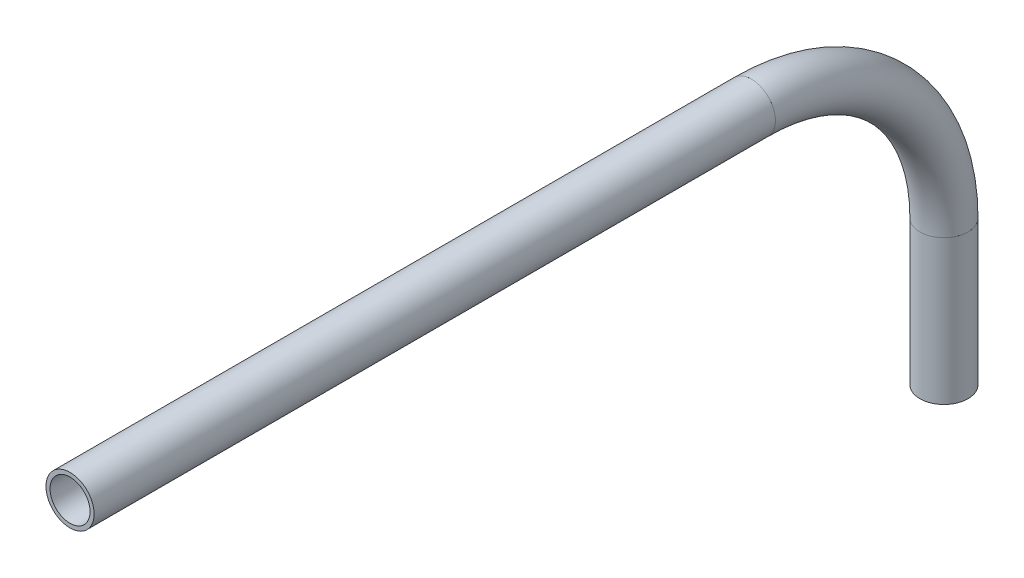
SolidWorks part; units mm, degrees
ref_plane "Front Plane" through (0, 0, 0) normal (0, 0, 1) x (1, 0, 0)
ref_plane "Top Plane" through (0, 0, 0) normal (0, 1, 0) x (1, 0, 0)
ref_plane "Right Plane" through (0, 0, 0) normal (1, 0, 0) x (0, 0, -1)
sketch "Sketch1" plane through (0, 0, 0) normal (1, 0, 0) x (0, 0, -1)
  line L1 (-129.6392, -232.8178) -> (-309.3187, -232.8178)
  line L2 (-78.8392, -283.6178) -> (-78.8392, -321.7178)
  arc A0 (-129.6392, -232.8178) -> (-78.8392, -283.6178) centre (-129.6392, -283.6178) cw
  dimension "D1" = 50.8
  dimension "D3" = 38.1
other "Pipe 0.5 SCH 40(1)"
ref_plane "Plane1" through (0, -283.6178, 78.8392) normal (0, -1, 0) x (0, 0, -1)
sketch "Sketch11" plane through (0, -283.6178, 78.8392) normal (0, -1, 0) x (0, 0, -1)
  circle A0 centre (0, 0) radius 5.2832
  circle A1 centre (0, 0) radius 6.35
  point P5 (0, 0)
  dimension "In_dia" = 10.5664
  dimension "Out_dia" = 12.7
